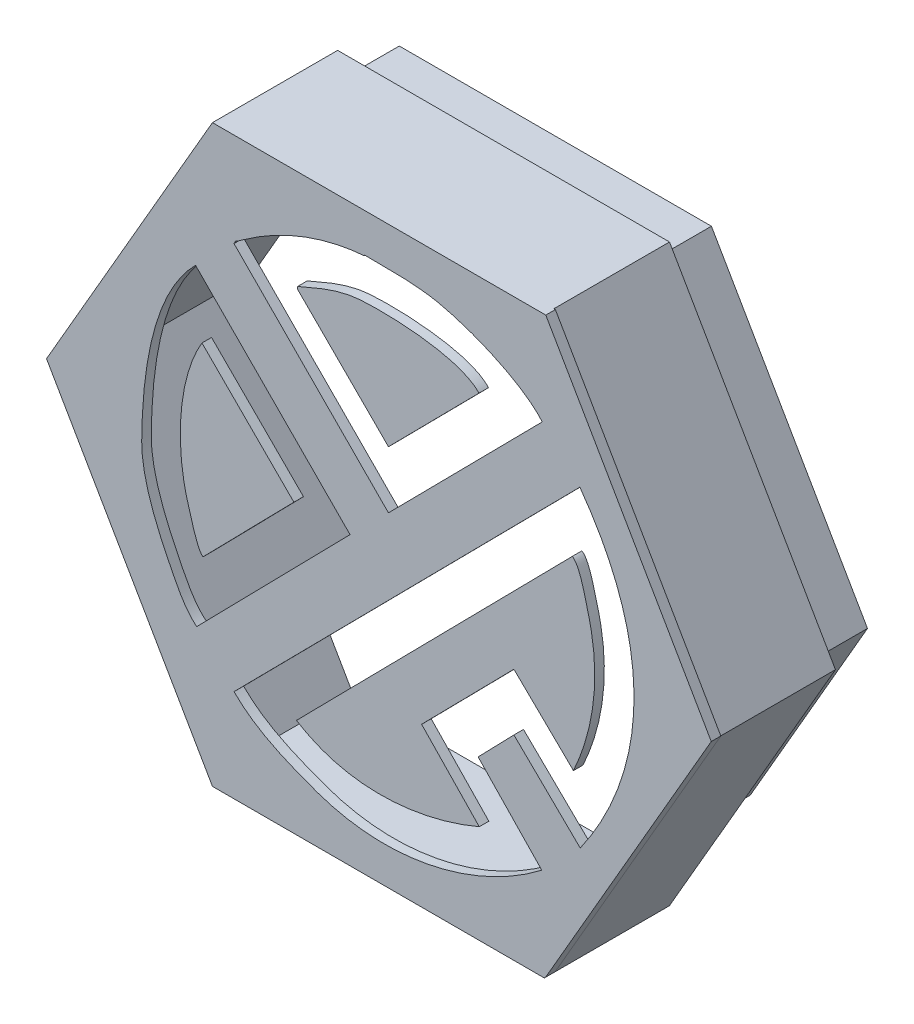
SolidWorks part; units mm, degrees
ref_plane "Front Plane" through (0, 0, 0) normal (0, 0, 1) x (1, 0, 0)
ref_plane "Top Plane" through (0, 0, 0) normal (0, 1, 0) x (1, 0, 0)
ref_plane "Right Plane" through (0, 0, 0) normal (1, 0, 0) x (0, 0, -1)
sketch "Sketch1" plane through (0, 0, 0) normal (0, 0, 1) x (1, 0, 0)
  line L0 (500, 1500) -> (2500, 1500) construction
  line L1 (440.4503, 1522.5381) -> (1325.2334, 1522.5381)
  line L2 (1325.2334, 1522.5381) -> (1764.4122, 761.8581)
  line L3 (1764.4122, 761.8581) -> (1324.5532, 0)
  line L4 (1324.5532, 0) -> (438.5875, 0)
  line L5 (438.5875, 0) -> (0, 759.6558)
  line L6 (0, 759.6558) -> (440.4503, 1522.5381)
  line L7 (1315.6202, 1272.1219) -> (907.6202, 859.1219)
  line L8 (907.6202, 859.1219) -> (497.6202, 1273.1219)
  line L9 (843.6202, 1418.1219) -> (843.6202, 1420.1219)
  line L10 (395.6202, 1172.1219) -> (805.6202, 758.1219)
  line L11 (805.6202, 758.1219) -> (398.6202, 343.1219)
  line L12 (1416.6202, 343.1219) -> (1240.6202, 515.1219)
  line L13 (1240.6202, 515.1219) -> (1145.6202, 417.1219)
  line L14 (1145.6202, 417.1219) -> (1314.6202, 241.1219)
  line L15 (497.6202, 243.1219) -> (1415.6202, 1172.1219)
  line L16 (412.6202, 1002.1219) -> (656.6202, 758.1219)
  line L17 (656.6202, 758.1219) -> (415.6202, 512.1219)
  line L18 (1147.6202, 1254.1219) -> (907.6202, 1011.1219)
  line L19 (907.6202, 1011.1219) -> (665.6202, 1253.1219)
  line L20 (665.6202, 1253.1219) -> (666.6202, 1259.1219)
  line L21 (1398.6202, 512.1219) -> (1240.6202, 666.1219)
  line L22 (1240.6202, 666.1219) -> (995.6202, 417.1219)
  line L23 (995.6202, 417.1219) -> (1148.6202, 258.1219)
  line L24 (663.6202, 260.1219) -> (1395.6202, 1003.1219)
  line L25 (0, 0) -> (0, 1449.5719) construction
  line L26 (0, 0) -> (2135.8585, 0) construction
  spline S0 degree 3 poles (843.6202, 1420.1219) (923.5458, 1418.8328) (948.3703, 1421.3241) (1012.6202, 1413.1219) (1100.1066, 1401.9535) (1260.881, 1339.0254) (1315.6202, 1272.1219) knots 0 0 0 0 1 1 1 2 2 2 2
  spline S1 degree 3 poles (497.6202, 1273.1219) (503.1728, 1284.2271) (498.3208, 1276.9272) (513.6202, 1288.1219) (611.1677, 1359.4981) (723.2205, 1408.3598) (843.6202, 1418.1219) knots 0 0 0 0 1 1 1 2 2 2 2
  spline S2 degree 3 poles (398.6202, 343.1219) (366.7692, 368.6028) (344.232, 415.8985) (326.6202, 451.1219) (290.2357, 523.891) (251.977, 614.4308) (252.6202, 696.1219) (253.8271, 849.3895) (277.8124, 1054.3141) (395.6202, 1172.1219) knots 0 0 0 0 1 1 1 2 2 2 3 3 3 3
  spline S3 degree 3 poles (1415.6202, 1172.1219) (1612.1543, 902.5895) (1602.2569, 607.1385) (1416.6202, 343.1219) knots 0 0 0 0 1 1 1 1
  spline S4 degree 3 poles (1314.6202, 241.1219) (1147.5957, 113.1883) (914.8363, 49.1955) (710.6202, 125.1219) (633.8534, 153.6635) (556.7228, 184.0194) (497.6202, 243.1219) knots 0 0 0 0 1 1 1 2 2 2 2
  spline S5 degree 3 poles (415.6202, 512.1219) (399.5558, 520.1541) (381.4821, 595.4945) (376.6202, 611.1219) (340.7948, 726.2753) (347.5892, 893.7369) (412.6202, 1002.1219) knots 0 0 0 0 1 1 1 2 2 2 2
  spline S6 degree 3 poles (666.6202, 1259.1219) (714.3797, 1279.9402) (768.4946, 1304.1075) (820.6202, 1310.1219) (887.1849, 1317.8025) (1095.844, 1313.2948) (1147.6202, 1254.1219) knots 0 0 0 0 1 1 1 2 2 2 2
  spline S7 degree 3 poles (1395.6202, 1003.1219) (1416.2077, 990.7695) (1428.1875, 928.8798) (1435.6202, 902.1219) (1472.6325, 768.8777) (1455.0842, 635.316) (1398.6202, 512.1219) knots 0 0 0 0 1 1 1 2 2 2 2
  spline S8 degree 3 poles (1148.6202, 258.1219) (1001.073, 194.8874) (808.0007, 168.2435) (663.6202, 260.1219) knots 0 0 0 0 1 1 1 1
  dimension "D1" = 120
  dimension "D2" = 120
  dimension "D3" = 120
  dimension "D4" = 120
  dimension "D5" = 120
  dimension "D6" = 120
  dimension "D7" = 885.9657
extrude "Boss-Extrude1" add sketch "Sketch1" along normal blind 25.4 contours S5 L0 L17 L16 | L0 S5 L17 | L5 L0 S2 L10 L11 L15 S3 L3 L2 L1 L6 L8 S1 L9 S0 L7 | L0 L5 L4 L3 S3 L12 L13 L14 S4 L15 L11 S2 | L0 L24 S8 L23 L22 | L24 L0 L22 L21 S7 | L0 L21 S7 | S6 L20 L19 L18
scale "Scale3" bodies to scale 103 101 102 104 scale about origin uniform scaling yes scale factor 0.057339
sketch "Sketch3" plane through (0, 0, 1.4564) normal (0, 0, 1) x (1, 0, 0)
  line L0 (25.2552, 87.3015) -> (75.9882, 87.3015) construction
  line L1 (75.7655, -0.185) -> (101.0207, 43.5582)
  line L2 (101.0207, 43.5582) -> (75.7655, 87.3015)
  line L3 (75.7655, 87.3015) -> (25.2552, 87.3015)
  line L4 (25.2552, 87.3015) -> (0, 43.5582)
  line L5 (0, 43.5582) -> (25.2552, -0.185)
  line L6 (25.2552, -0.185) -> (75.7655, -0.185)
  line L7 (25.1484, 0) -> (0, 43.5582) construction
  line L8 (0, 43.5582) -> (25.2552, 87.3015) construction
  line L10 (98.0878, 43.5582) -> (74.2991, 84.7615)
  line L11 (74.2991, 84.7615) -> (26.7216, 84.7615)
  line L12 (26.7216, 84.7615) -> (2.9329, 43.5582)
  line L13 (2.9329, 43.5582) -> (26.7216, 2.355)
  line L14 (26.7216, 2.355) -> (74.2991, 2.355)
  line L15 (74.2991, 2.355) -> (98.0878, 43.5582)
  circle A0 centre (50.5104, 43.5582) radius 43.7432 construction
  circle A1 centre (50.5104, 43.5582) radius 41.2032 construction
  dimension "D1" = 2.54
  dimension "D2" = 2.54
extrude "Boss-Extrude2" add sketch "Sketch3" against normal blind 19.05
sketch "Sketch4" plane through (0, 0, 0) normal (0, 0, 1) x (1, 0, 0)
  line L0 (0, 43.5582) -> (101.1704, 43.6845) construction
  line L2 (74.3375, 2.4813) -> (98.0897, 43.6214)
  line L3 (98.0897, 43.6214) -> (74.3375, 84.7615)
  line L4 (74.3375, 84.7615) -> (26.833, 84.7615)
  line L5 (26.833, 84.7615) -> (3.0807, 43.6214)
  line L6 (3.0807, 43.6214) -> (26.833, 2.4813)
  line L7 (26.833, 2.4813) -> (74.3375, 2.4813)
  line L8 (25.2552, 87.3015) -> (75.9882, 87.3015) construction
  line L10 (73.6042, 3.7513) -> (96.6232, 43.6214)
  line L11 (96.6232, 43.6214) -> (73.6042, 83.4915)
  line L12 (73.6042, 83.4915) -> (27.5662, 83.4915)
  line L13 (27.5662, 83.4915) -> (4.5472, 43.6214)
  line L14 (4.5472, 43.6214) -> (27.5662, 3.7513)
  line L15 (27.5662, 3.7513) -> (73.6042, 3.7513)
  circle A0 centre (50.5852, 43.6214) radius 41.1401 construction
  circle A1 centre (50.5852, 43.6214) radius 39.8701 construction
  dimension "D1" = 2.54
  dimension "D2" = 1.27
extrude "Boss-Extrude3" add sketch "Sketch4" against normal blind 25.4
sketch "Sketch5" plane through (0, 0, 0) normal (0, 1, 0) x (1, 0, 0)
  line L0 (12.6276, -16.4764) -> (12.6276, 33.0078) construction
  line L1 (88.3931, -14.5973) -> (88.3931, 35.409) construction
  line L2 (0, -1.4564) -> (0, 17.5936) construction
  line L3 (25.2552, 17.5936) -> (25.2552, -1.4564) construction
  line L4 (75.7655, 17.5936) -> (75.7655, -1.4564) construction
  line L5 (101.0207, 17.5936) -> (101.0207, 0) construction
  line L7 (12.6276, 17.5658) -> (88.3931, 17.5658)
  line L8 (12.6276, 17.5658) -> (12.6276, 25.4403)
  line L9 (12.6276, 25.4403) -> (88.3931, 25.4403)
  line L10 (88.3931, 17.5658) -> (88.3931, 25.4403)
extrude "Cut-Extrude1" cut sketch "Sketch5" along normal blind 12.7
